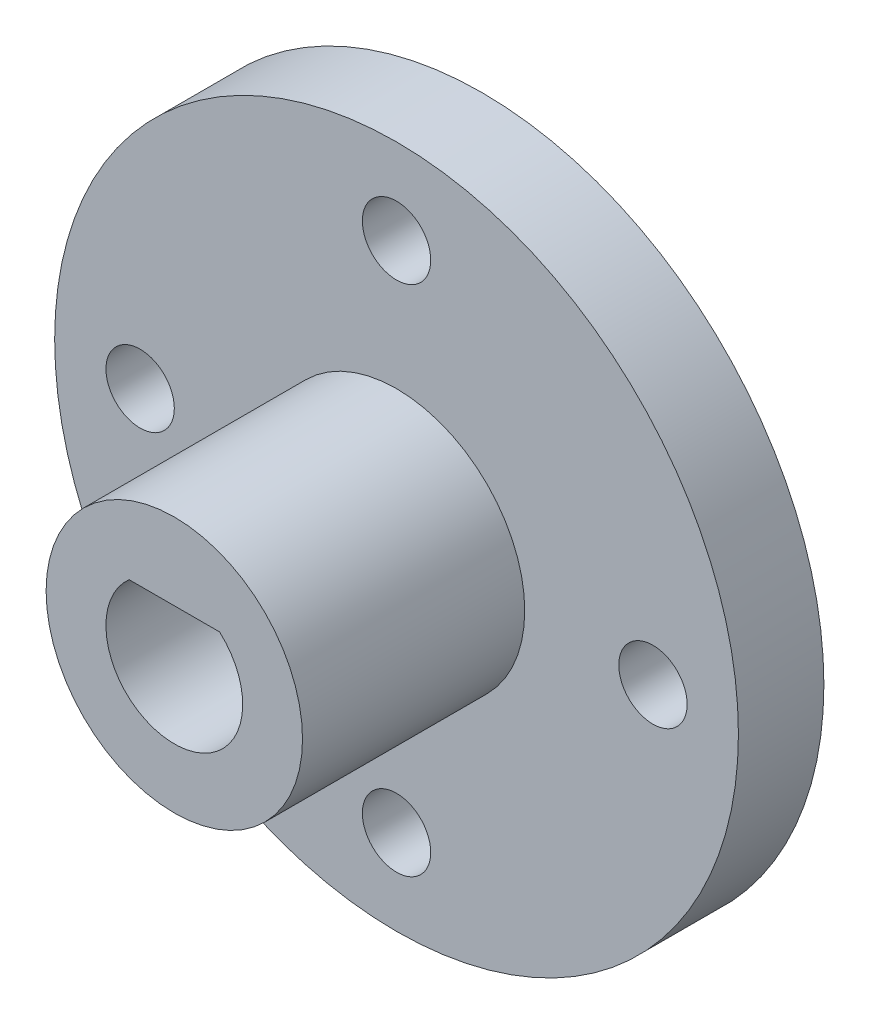
SolidWorks part; units mm, degrees
ref_plane "Front Plane" through (0, 0, 0) normal (0, 0, 1) x (1, 0, 0)
ref_plane "Top Plane" through (0, 0, 0) normal (0, 1, 0) x (1, 0, 0)
ref_plane "Right Plane" through (0, 0, 0) normal (1, 0, 0) x (0, 0, -1)
sketch "Sketch1" plane through (0, 0, 0) normal (0, 0, 1) x (1, 0, 0)
  circle A0 centre (0, 0) radius 20
  dimension "D1" = 40
extrude "Boss-Extrude1" add sketch "Sketch1" along normal blind 5
sketch "Sketch2" plane through (0, 0, 5) normal (0, 0, 1) x (1, 0, 0)
  circle A0 centre (0, 0) radius 7.5
  dimension "D1" = 15
extrude "Boss-Extrude2" add sketch "Sketch2" along normal blind 13
sketch "Sketch3" plane through (0, 0, 18) normal (0, 0, 1) x (1, 0, 0)
  line L0 (-2.6458, 3) -> (2.6458, 3)
  arc A0 (-2.6458, 3) -> (2.6458, 3) centre (0, 0) ccw
  dimension "D1" = 8
  dimension "D2" = 3
extrude "Cut-Extrude1" cut sketch "Sketch3" against normal blind 18
sketch "Sketch4" plane through (0, 0, 5) normal (0, 0, 1) x (1, 0, 0)
  circle A0 centre (0, 0) radius 15 construction
  circle A1 centre (0, 15) radius 2
  circle A2 centre (15, 0) radius 2
  circle A3 centre (0, -15) radius 2
  circle A4 centre (-15, 0) radius 2
  point P14 (0, 0)
  dimension "D1" = 30
  dimension "D2" = 4
  dimension "D3" = 4
extrude "Cut-Extrude2" cut sketch "Sketch4" against normal blind 18
